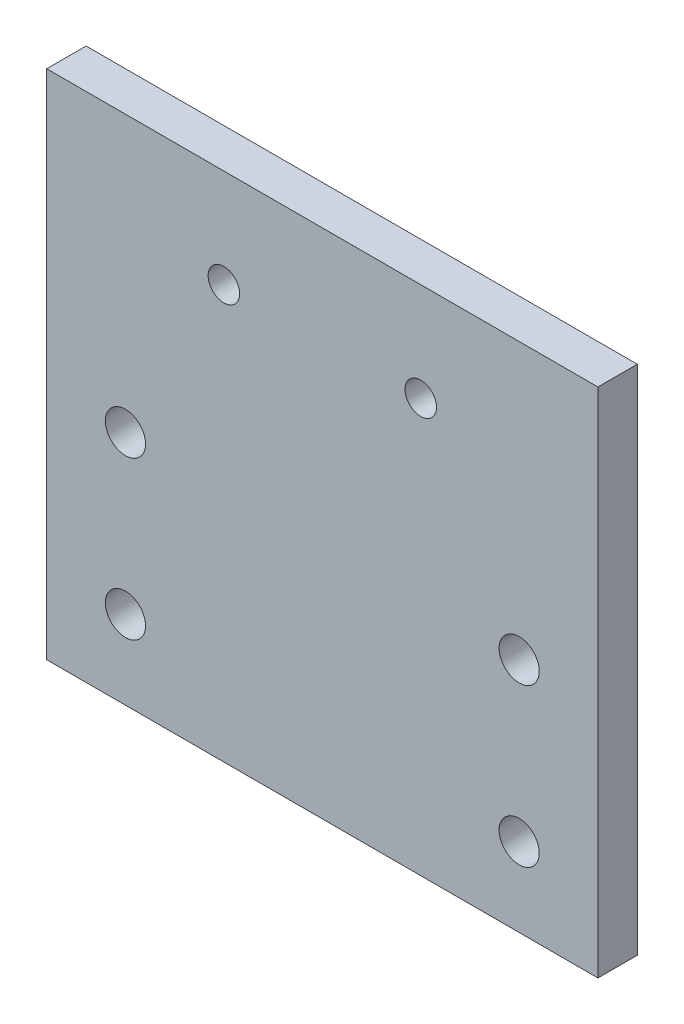
SolidWorks part; units mm, degrees
ref_plane "Front Plane" through (0, 0, 0) normal (0, 0, 1) x (1, 0, 0)
ref_plane "Top Plane" through (0, 0, 0) normal (0, 1, 0) x (1, 0, 0)
ref_plane "Right Plane" through (0, 0, 0) normal (1, 0, 0) x (0, 0, -1)
sketch "Sketch1" plane through (0, 0, 0) normal (0, 0, 1) x (1, 0, 0)
  line L0 (-35, -12.5) -> (-35, -52.5)
  line L1 (-30, -7.5) -> (30, -7.5) construction
  line L2 (-30, -7.5) -> (-30, 7.5) construction
  line L3 (-30, 7.5) -> (30, 7.5) construction
  line L4 (30, -7.5) -> (30, 7.5) construction
  line L5 (-30, -7.5) -> (30, 7.5) construction
  line L6 (-30, 7.5) -> (30, -7.5) construction
  line L7 (-35, -12.5) -> (35, -12.5) construction
  line L8 (-35, -12.5) -> (-35, 12.5)
  line L9 (-35, 12.5) -> (35, 12.5)
  line L10 (35, -12.5) -> (35, 12.5)
  line L11 (-35, -12.5) -> (35, 12.5) construction
  line L12 (-35, 12.5) -> (35, -12.5) construction
  line L13 (-35, -52.5) -> (35, -52.5)
  line L14 (35, -52.5) -> (35, -12.5)
  line L15 (0, 12.5) -> (0, -52.5) construction
  line L16 (-35, -22.5) -> (35, -22.5) construction
  line L17 (-35, -42.5) -> (35, -42.5) construction
  line L18 (35, 0) -> (-35, 0) construction
  circle A0 centre (-25, -22.5) radius 2.55
  circle A1 centre (-25, -42.5) radius 2.55
  circle A2 centre (25, -42.5) radius 2.55
  circle A3 centre (25, -22.5) radius 2.55
  circle A4 centre (-12.5, 0) radius 2
  circle A5 centre (12.5, 0) radius 2
  point P0 (0, 0)
  point P5 (0, 0)
  point P31 (-13.696, 0)
  dimension "D6" = 5.1
  dimension "D7" = 5.1
  dimension "D8" = 25
  dimension "D9" = 25
  dimension "D12" = 4
  dimension "D13" = 25
  dimension "D1" = 15
  dimension "D2" = 60
  dimension "D3" = 5
  dimension "D4" = 5
  dimension "D5" = 40
  dimension "D10" = 10
  dimension "D11" = 30
extrude "Boss-Extrude1" add sketch "Sketch1" along normal blind 5 contours L9 L10 L14 L13 L0 L8
